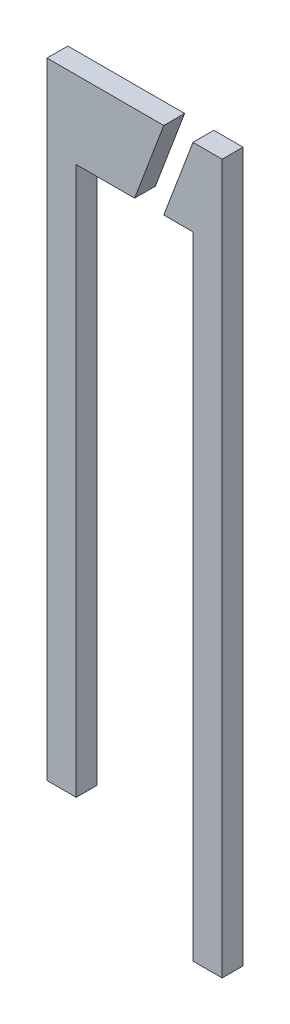
SolidWorks part; units mm, degrees
ref_plane "Front Plane" through (0, 0, 0) normal (0, 0, 1) x (1, 0, 0)
ref_plane "Top Plane" through (0, 0, 0) normal (0, 1, 0) x (1, 0, 0)
ref_plane "Right Plane" through (0, 0, 0) normal (1, 0, 0) x (0, 0, -1)
sketch "Sketch1" plane through (0, 0, 0) normal (0, 0, 1) x (1, 0, 0)
  line L0 (1.4, 5.2836) -> (0.7, 3.4235)
  line L1 (0.7, 3.4235) -> (1.4, 3.4235)
  line L2 (1.4, 3.4235) -> (1.4, -11.7164)
  line L3 (1.4, -11.7164) -> (2.1, -11.7164)
  line L4 (2.1, -11.7164) -> (2.1, 5.2836)
  line L5 (2.1, 5.2836) -> (1.4, 5.2836)
  line L6 (-2.1, -9.7164) -> (-1.4, -9.7164)
  line L7 (-1.4, -9.7164) -> (-1.4, 3.4235)
  line L8 (-1.4, 3.4235) -> (0, 3.4235)
  line L9 (0, 3.4235) -> (0.7, 5.2836)
  line L10 (0.7, 5.2836) -> (-2.1, 5.2836)
  line L11 (-2.1, 5.2836) -> (-2.1, -9.7164)
  line L12 (0, 10.4288) -> (0, -15.2177) construction
  dimension "D1" = 15
  dimension "D2" = 17
  dimension "D3" = 0.7
  dimension "D4" = 0.7
  dimension "D5" = 0.7
  dimension "D6" = 0.7
  dimension "D7" = 1.4
  dimension "D8" = 0.7
  dimension "D9" = 0.7
extrude "Boss-Extrude1" add sketch "Sketch1" along normal blind 0.5
